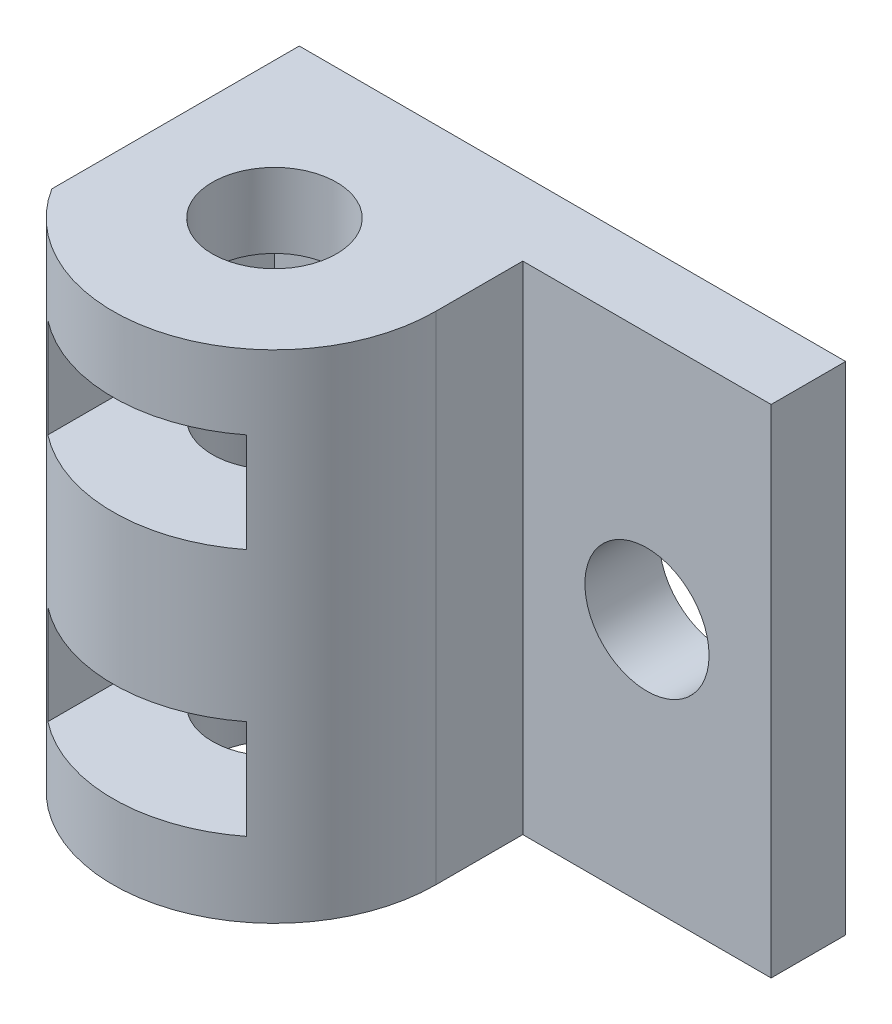
SolidWorks part; units mm, degrees
ref_plane "Front Plane" through (0, 0, 0) normal (0, 0, 1) x (1, 0, 0)
ref_plane "Top Plane" through (0, 0, 0) normal (0, 1, 0) x (1, 0, 0)
ref_plane "Right Plane" through (0, 0, 0) normal (1, 0, 0) x (0, 0, -1)
sketch "Sketch1" plane through (0, 0, 0) normal (0, 0, 1) x (1, 0, 0)
  line L1 (-10.5595, 5.237) -> (12.4405, 5.237)
  line L2 (-10.5595, 5.237) -> (-10.5595, -14.763)
  line L3 (-10.5595, -14.763) -> (12.4405, -14.763)
  line L4 (12.4405, 5.237) -> (12.4405, -14.763)
  dimension "D1" = 23
  dimension "D2" = 20
extrude "Boss-Extrude1" add sketch "Sketch1" along normal blind 3
sketch "Sketch2" plane through (0, 5.237, 0) normal (0, 1, 0) x (1, 0, 0)
  line L0 (12.4405, 0) -> (-10.5595, 0) construction
  line L1 (-10.5595, -3) -> (-10.5595, 0) construction
  line L2 (-4.0595, 0) -> (-4.0595, -13)
  line L3 (-10.5595, -3) -> (-10.5595, -6.5)
  line L4 (2.4405, -6.5) -> (2.4405, -3)
  line L5 (12.4405, -3) -> (-10.5595, -3) construction
  circle A0 centre (-4.0595, -6.5) radius 6.5
  circle A1 centre (-4.0595, -6.5) radius 2.5
  point P9 (-4.0595, -8.497)
  point P10 (-4.0595, -4.5)
  line M4 (-10.5595, -3) -> (12.4405, -3)
  dimension "D1" = 13
  dimension "D2" = 5
extrude "Boss-Extrude2" add sketch "Sketch2" against normal through all contours L2 A0 M4 | A1 L2 A0 M4 | A1 L2 A0 M4 | A0 L2 M4 | A0 L3 M4 | A0 L4 M4
ref_plane "Plane1" through (0, 0.237, 0) normal (0, -1, 0) x (-1, 0, 0)
sketch "Sketch4" plane through (0, 0.237, 0) normal (0, -1, 0) x (-1, 0, 0)
  line L0 (8.0595, -2.5) -> (0.0595, -10.5) construction
  line L1 (0.0595, -2.5) -> (8.0595, -2.5)
  line L2 (0.0595, -2.5) -> (0.0595, -10.5)
  line L4 (8.0595, -2.5) -> (8.0595, -10.5)
  line L5 (0.0595, -2.5) -> (8.0595, -10.5) construction
  line L8 (0.0595, -10.5) -> (0.0595, -14.5708)
  line L9 (0.0595, -14.5708) -> (8.0595, -14.5708)
  line L10 (8.0595, -10.5) -> (8.0595, -14.5708)
  circle A0 centre (4.0595, -6.5) radius 2.5 construction
  point P6 (4.0595, -6.5)
  dimension "D1" = 8
  dimension "D2" = 8
extrude "Cut-Extrude2" cut sketch "Sketch4" against normal mid plane 4 contours L9 L10 L4 L1 L2 L8
sketch "Sketch5" plane through (0, 0, 0) normal (0, 0, -1) x (-1, 0, 0)
  line L0 (-12.4405, -4.763) -> (10.5595, -4.763) construction
  line L1 (-12.4405, -14.763) -> (-12.4405, 5.237) construction
  line L2 (10.5595, 5.237) -> (10.5595, -14.763) construction
pattern_linear "LPattern2" count 2 spacing 10 along (0, -1, 0) of "Cut-Extrude2"
sketch "Sketch6" plane through (0, 0, 3) normal (0, 0, 1) x (1, 0, 0)
  line L0 (7.4405, 5.237) -> (7.4405, -14.763) construction
  line L1 (12.4405, 5.237) -> (2.4405, 5.237) construction
  line L2 (2.4405, -14.763) -> (12.4405, -14.763) construction
  circle A0 centre (7.4405, -4.763) radius 2.5
  dimension "D1" = 5
extrude "Cut-Extrude3" cut sketch "Sketch6" against normal blind 4
sketch "Sketch7" plane through (-10.5595, 0, 0) normal (-1, 0, 0) x (0, 0, 1)
  line L1 (0, 5.237) -> (15.3593, 5.237)
  line L2 (0, 5.237) -> (0, -14.763)
  line L3 (0, -14.763) -> (15.3593, -14.763)
  line L4 (15.3593, 5.237) -> (15.3593, -14.763)
extrude "Cut-Extrude4" cut sketch "Sketch7" against normal blind 1 contours L4 L3 L2 L1
